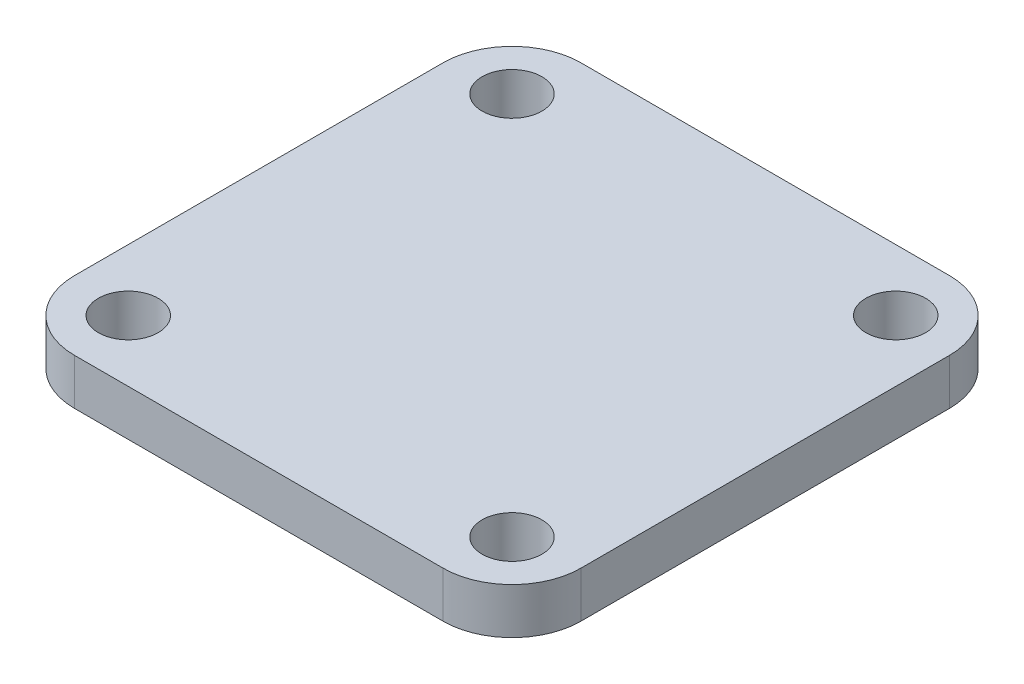
SolidWorks part; units mm, degrees
ref_plane "Front Plane" through (0, 0, 0) normal (0, 0, 1) x (1, 0, 0)
ref_plane "Top Plane" through (0, 0, 0) normal (0, 1, 0) x (1, 0, 0)
ref_plane "Right Plane" through (0, 0, 0) normal (1, 0, 0) x (0, 0, -1)
sketch "Sketch1" plane through (0, 0, 0) normal (0, 1, 0) x (1, 0, 0)
  line L1 (-27.55, -27.55) -> (27.55, -27.55)
  line L2 (-27.55, -27.55) -> (-27.55, 27.55)
  line L3 (-27.55, 27.55) -> (27.55, 27.55)
  line L4 (27.55, -27.55) -> (27.55, 27.55)
  line L5 (-27.55, -27.55) -> (27.55, 27.55) construction
  line L6 (-27.55, 27.55) -> (27.55, -27.55) construction
  circle A0 centre (20.87, -20.87) radius 3.25
  circle A1 centre (-20.87, -20.87) radius 3.25
  circle A2 centre (-20.87, 20.87) radius 3.25
  circle A3 centre (20.87, 20.87) radius 3.25
  point P0 (0, 0)
  dimension "D1" = 55.1
  dimension "D2" = 55.1
extrude "Boss-Extrude1" add sketch "Sketch1" along normal blind 5
fillet "Fillet1" radius 7.5 4 edges at (-27.55, 2.5, -27.55) (-27.55, 2.5, 27.55) (27.55, 2.5, 27.55) (27.55, 2.5, -27.55)
